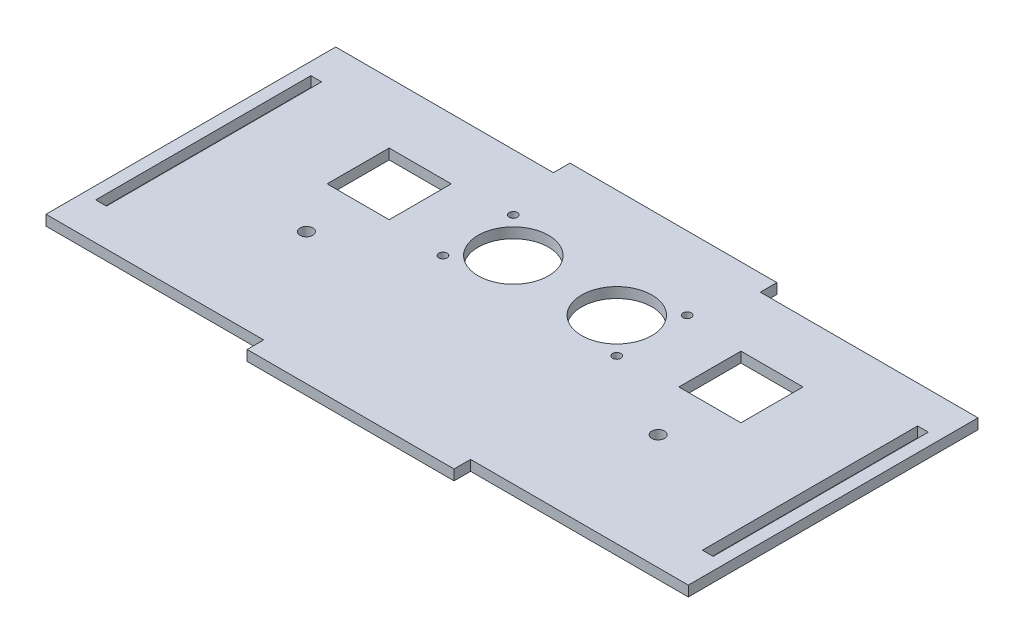
SolidWorks part; units mm, degrees
ref_plane "Front Plane" through (0, 0, 0) normal (0, 0, 1) x (1, 0, 0)
ref_plane "Top Plane" through (0, 0, 0) normal (0, 1, 0) x (1, 0, 0)
ref_plane "Right Plane" through (0, 0, 0) normal (1, 0, 0) x (0, 0, -1)
sketch "Sketch2" plane through (0, 0, 0) normal (0, 1, 0) x (1, 0, 0)
  line L0 (-25, 35) -> (-77.6, 35)
  line L1 (-77.6, 35) -> (-77.6, -35)
  line L2 (-77.6, -35) -> (-25, -35)
  line L3 (-25, -35) -> (-25, -39)
  line L4 (-25, -39) -> (25, -39)
  line L5 (-74.6, 26) -> (-72, 26)
  line L6 (-72, -26) -> (-72, 26)
  line L7 (-74.6, -26) -> (-72, -26)
  line L8 (-74.6, -26) -> (-74.6, 26)
  line L9 (0, -112.7216) -> (0, 112.7216) construction
  line L10 (85.5857, 0) -> (-85.5857, 0) construction
  line L11 (25, 35) -> (77.6, 35)
  line L12 (74.6, -26) -> (74.6, 26)
  line L13 (74.6, -26) -> (72, -26)
  line L14 (72, -26) -> (72, 26)
  line L15 (74.6, 26) -> (72, 26)
  line L16 (77.6, 35) -> (77.6, -35)
  line L17 (77.6, -35) -> (25, -35)
  line L18 (25, -35) -> (25, -39)
  line L19 (25, 35) -> (25, 39)
  line L20 (-25, 35) -> (-25, 39)
  line L21 (-25, 39) -> (25, 39)
  line L22 (-28.5048, 12.8182) -> (28.5048, 12.8182) construction
  line L27 (0, -1.7183) -> (0, 27.3547) construction
  line L28 (-35, 5.3182) -> (-50, 20.3182) construction
  line L29 (35, 5.3182) -> (50, 5.3182)
  line L30 (35, 5.3182) -> (35, 20.3182)
  line L31 (35, 20.3182) -> (50, 20.3182)
  line L32 (50, 5.3182) -> (50, 20.3182)
  line L33 (35, 5.3182) -> (50, 20.3182) construction
  line L34 (35, 20.3182) -> (50, 5.3182) construction
  line L35 (-35, 20.3182) -> (-50, 5.3182) construction
  line L36 (-35, 20.3182) -> (-50, 20.3182)
  line L37 (-50, 5.3182) -> (-50, 20.3182)
  line L38 (-35, 5.3182) -> (-50, 5.3182)
  line L39 (-35, 5.3182) -> (-35, 20.3182)
  circle A0 centre (-12.5, 12.8182) radius 8.5
  circle A2 centre (-21, 21.3182) radius 1
  circle A3 centre (-21, 4.3182) radius 1
  circle A4 centre (21, 4.3182) radius 1
  circle A5 centre (21, 21.3182) radius 1
  circle A7 centre (12.5, 12.8182) radius 8.5
  circle A8 centre (-42.5, -7.1818) radius 1.55
  circle A9 centre (42.5, -7.1818) radius 1.55
  point P0 (42.5, 12.8182)
  point P1 (-77.6, 0)
  point P20 (0, 0)
  point P23 (0, 0)
  point P29 (0, 112.7216)
  point P43 (0, 12.8182)
  point P45 (0, 12.8182)
  dimension "D14" = 17
  dimension "D15" = 15
  dimension "D16" = 2
  dimension "D8" = 17
  dimension "D11" = 25
  dimension "D12" = 8.5
  dimension "D21" = 3.1
  dimension "D1" = 4
  dimension "D2" = 25
  dimension "D3" = 2.6
  dimension "D4" = 2.6
  dimension "D5" = 3
  dimension "D6" = 70
  dimension "D7" = 35
  dimension "D9" = 52
  dimension "D10" = 26
  dimension "D13" = 15
  dimension "D17" = 0
  dimension "D18" = 35
  dimension "D19" = 14.6818
  dimension "D20" = 12.5
extrude "Boss-Extrude1" add sketch "Sketch2" along normal blind 2.5
